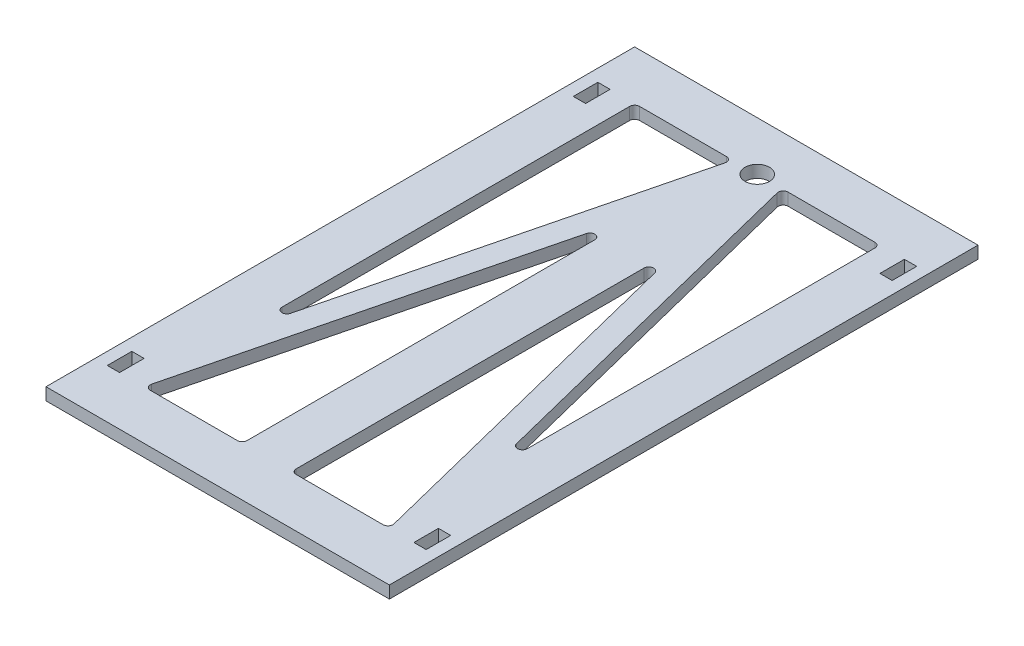
SolidWorks part; units mm, degrees
material "Beech"
ref_plane "Front Plane" through (0, 0, 0) normal (0, 0, 1) x (1, 0, 0)
ref_plane "Top Plane" through (0, 0, 0) normal (0, 1, 0) x (1, 0, 0)
ref_plane "Right Plane" through (0, 0, 0) normal (1, 0, 0) x (0, 0, -1)
sketch "Sketch1" plane through (0, 0, 0) normal (0, 1, 0) x (1, 0, 0)
  line L0 (0, 0) -> (177.8, 0)
  line L1 (0, 0) -> (0, 304.8)
  line L2 (177.8, 0) -> (177.8, 304.8)
  line L3 (0, 304.8) -> (177.8, 304.8)
  line L4 (0, 0) -> (12.7, 0)
  line L8 (177.8, 0) -> (165.1, 0)
  line L12 (127, 0) -> (114.3, 0)
  line L16 (50.8, 0) -> (63.5, 0)
  line L20 (165.1, 279.4) -> (171.45, 279.4)
  line L21 (165.1, 279.4) -> (165.1, 266.7)
  line L22 (171.45, 279.4) -> (171.45, 266.7)
  line L23 (165.1, 266.7) -> (171.45, 266.7)
  line L24 (6.35, 279.4) -> (12.7, 279.4)
  line L25 (6.35, 279.4) -> (6.35, 266.7)
  line L26 (12.7, 279.4) -> (12.7, 266.7)
  line L27 (6.35, 266.7) -> (12.7, 266.7)
  line L28 (6.35, 38.1) -> (12.7, 38.1)
  line L29 (6.35, 38.1) -> (6.35, 25.4)
  line L30 (12.7, 38.1) -> (12.7, 25.4)
  line L31 (6.35, 25.4) -> (12.7, 25.4)
  line L32 (165.1, 38.1) -> (171.45, 38.1)
  line L33 (165.1, 38.1) -> (165.1, 25.4)
  line L34 (171.45, 38.1) -> (171.45, 25.4)
  line L35 (165.1, 25.4) -> (171.45, 25.4)
  line L36 (101.6, 279.4) -> (152.4, 279.4)
  line L37 (152.4, 279.4) -> (152.4, 76.2)
  line L38 (152.4, 76.2) -> (101.6, 279.4)
  line L39 (101.6, 228.6) -> (101.6, 25.4)
  line L40 (101.6, 25.4) -> (152.4, 25.4)
  line L41 (152.4, 25.4) -> (101.6, 228.6)
  line L42 (76.2, 279.4) -> (25.4, 279.4)
  line L43 (25.4, 279.4) -> (25.4, 76.2)
  line L44 (25.4, 76.2) -> (76.2, 279.4)
  line L45 (76.2, 228.6) -> (76.2, 25.4)
  line L46 (76.2, 25.4) -> (25.4, 25.4)
  line L47 (25.4, 25.4) -> (76.2, 228.6)
  circle A0 centre (88.9, 279.4) radius 6.35
  point P21 (88.9, 304.8)
  dimension "D8" = 12.7
  dimension "D1" = 177.8
  dimension "D6" = 304.8
  dimension "D7" = 25.4
  dimension "D9" = 25.4
  dimension "D10" = 25.4
  dimension "D11" = 12.7
  dimension "D12" = 12.7
  dimension "D13" = 203.2
  dimension "D14" = 50.8
  dimension "D15" = 50.8
extrude "Front Panel" add sketch "Sketch1" along normal blind 6.35
fillet "Fillet1" radius 2.54 12 edges at (25.4, 3.175, -76.2) (152.4, 3.175, -76.2) (25.4, 3.175, -25.4) (76.2, 3.175, -25.4) (101.6, 3.175, -25.4) (152.4, 3.175, -25.4) (76.2, 3.175, -228.6) (101.6, 3.175, -228.6) (25.4, 3.175, -279.4) (76.2, 3.175, -279.4) (101.6, 3.175, -279.4) (152.4, 3.175, -279.4)
equation "\"CageLeftBottomEdge\"=22.11mm"
equation "\"CageLeftTopEdge\"=22.11mm"
equation "\"CageRightBottomEdge\"=21.63mm"
equation "\"CageRightTopEdge\"=21.63mm"
equation "\"CageHeight\"=86.04mm"
equation "\"CageLength\"=73.76mm"
equation "\"CageTopScrewClearance\"=10mm"
equation "\"CageBottomScrewClearance\"=25mm"
equation "\"CageLeftTopDepth\"= 11.65mm"
equation "\"CageLeftBottomDepth\"=11.11mm"
equation "\"CageLeftTopHeight\"=8.56175mm"
equation "\"CageLeftBottomHeight\"=16mm"
equation "\"CageRightTopDepth\"= 11.05mm"
equation "\"CageRightBottomDepth\"=10.58mm"
equation "\"CageRightTopHeight\"=9.6mm"
equation "\"CageRightBottomHeight\"=15.49mm"
equation "\"CageLeftTopChannelDepth\"=2.41908mm"
equation "\"CageLeftBottomChannelDepth\"=2.588mm"
equation "\"CageLeftChannelHeight\"=11.7mm"
equation "\"CageRightTopChannelDepth\"=2.32mm"
equation "\"CageRightBottomChannelDepth\"=2.318mm"
equation "\"CageRightChannelHeight\"=10mm"
equation "\"CageChanRelHeight\"=23.99mm"
equation "\"CageChanRelDepth\"=5.492mm"
equation "\"CageChamberRadius\"=16.261mm"
equation "\"CageScrewDiameter\"=4.8mm"
equation "\"CageSetScrewDiameter\"=3.5mm"
equation "\"CageAxleRadius\"=6.639mm"
equation "\"CageAxleKeyHeight\"=1.619mm"
equation "\"CageAxleKeyWidth\"=2.662mm"
equation "\"CageHoseWindowWidth\"=16.29mm"
equation "\"CageHoseWindowHeight\"=26.5mm"
equation "\"CageHoseWindow-Edge\"=8.89mm"
equation "\"CageScrew-VerticalEdge\"=5.0mm"
equation "\"CageScrew-HorizontalEdge\"=7.5mm"
equation "\"CageScrew-HoseCornerScrewEdge\"=4.45mm"
equation "\"CageAxle-BottomEdge\"=56.05mm"
equation "\"CageAxle-FrontEdge\"=46.03mm"
equation "\"CageBackSetScrew-Axle\"=40mm"
equation "\"CageFrontSetScrew-Axle\"=22mm"
equation "\"CageVelocityWindow-BackEdge\"=34.8mm"
equation "\"CageVelocityWindow-BottomEdge\"=27.55mm"
equation "\"CageVelocityWindowHeight\"=22.29mm"
equation "\"CageVelocityWindowWidth\"=12.61mm"
equation "\"TriggerSlot-BottomEdge\"=6.35mm"
equation "\"TriggerSlot-FrontEdge\"=15mm"
equation "\"TriggerSlotSize\"=6.7mm"
equation "\"TriggerRackOffset\"=6mm"
equation "\"TriggerSlotSizeInt\"=.25in"
equation "\"MotorMountLegLength\"=.25in"
equation "\"GearOffset\"=.264907in"
equation "\"TriggerSlotSpacing\"=.25in"
equation "\"TriggerMiniSlotWidth\"=3.5mm"
equation "\"TriggerRackWidth\"=6.5mm"
equation "\"pandiscradius\"=14in"
equation "\"towermaterialwidth\"=.25in"
equation "\"towerslotlength\"=.5in"
equation "\"towermarkerspace\"=5in"
equation "\"towerslothorizoffset\"=1in"
equation "\"towerslothorizspacing\"=2in"
equation "\"towerslotvertoffset\"=3in"
equation "\"towerslotvertspacing\"=1in"
equation "\"towerheight\"=12in"
equation "\"towerupslot\"=1in"
equation "\"D1@Sketch1\"=(\"towerslothorizoffset\"+\"towerslothorizspacing\"+\"towerslotlength\")*2"
equation "\"D6@Sketch1\"=\"towerheight\""
equation "\"D7@Sketch1\"=\"towerupslot\""
equation "\"toweraxle\"=.5in"
equation "\"D8@Sketch1\"=\"toweraxle\""
equation "\"D9@Sketch1\"=\"towerupslot\""
equation "\"D10@Sketch1\"= \"towerupslot\""
equation "\"D1@Front Panel\"=\"towermaterialwidth\""
equation "\"stepperouterrad\"=10mm"
equation "\"stepperscrewsize\"=3.45mm"
equation "\"stepperscrewc2c\"=49.5mm"
equation "\"stepperdepthoffset\"=24mm"
equation "\"stepperhorizoffset\"=22.91mm"
equation "\"shaftslotOD\"=18.8mm"
equation "\"shaftslotID\"=13.28mm"
equation "\"shaftkeywidth\"=2.67mm"
equation "\"shaftkeydepth\"=1.8mm"
equation "\"shaftcollartotaldepth\"=9.71mm"
equation "\"shaftsquaredepth\"=6mm"
equation "\"shaftsetscrewsize\"=3.5mm"
equation "\"shaftkeytightdepth\"=1.85mm"
equation "\"shaftslottightID\"=12.78mm"
equation "\"shaftsetscrewoffset\"=9mm"
equation "\"cagecollartotaldepth\"=20mm"
equation "\"cagecollartotalwidth\"=35mm"
equation "\"cagecollarbasedepth\"=4mm"
equation "\"D11@Sketch1\"=\"toweraxle\""
equation "\"D12@Sketch1\"=\"toweraxle\""
equation "\"towerspeedwidth\"=2in"
equation "\"D15@Sketch1\"=\"towerspeedwidth\""
equation "\"towerspeedheight\"=8in"
equation "\"D13@Sketch1\"=\"towerspeedheight\""
equation "\"towerspeedgap\"=2in"
equation "\"D14@Sketch1\"=\"towerspeedgap\""
equation "\"gearhubintdiam\"=30mm"
equation "\"gearhubintwid\"=12.21mm"
equation "\"stepperaxleflat\"=.037in"
equation "\"stepperaxlerad\"=0.11811024in"
equation "\"ajaxaxlesize\"=3.87mm"
equation "\"ajaxinnercut\"=2.3mm"
equation "\"ajaxwidth\"=6.1mm"
equation "\"ajaxdiametral\"=25.8854"
equation "\"ajaxcutoutdepth\"=2.3mm"
equation "\"ajax4020gap\"=29.5mm"
equation "\"ajax4010gap\"=24.5mm"
equation "\"ajax20hubbuffer\"=6.1mm"
equation "\"ajax20hubholeoffset\"=.19685in"
equation "\"ajax20hubholesize\"=.059055in"
equation "\"ajax20cutoutint\"=13.4mm"
equation "\"ajax40hubholesize\"=7.21mm"
equation "\"ajax40hubholeoffset\"=10mm"
equation "\"ajax40hubbuffer\"=8.9mm"
equation "\"ajax40cutoutint\"=32.6mm"
equation "\"bearingpandiscrad\"=6.8in"
equation "\"bearingpandiscang\"=48.75deg"
equation "\"bearingclearholedist\"=4.7345in"
equation "\"bearingclearholesize\"=.5in"
equation "\"bearingclearholeang\"=22.5deg"
equation "\"bearingmountholedist\"=4.25in"
equation "\"bearingwirehole\"=1.5in"
equation "\"no6diam\"=.146in"
equation "\"shortconangle\"=20deg"
equation "\"shortconlen\"=.875in"
equation "\"longconlen\"=1.25in"
equation "\"longconangle\"=15deg"
